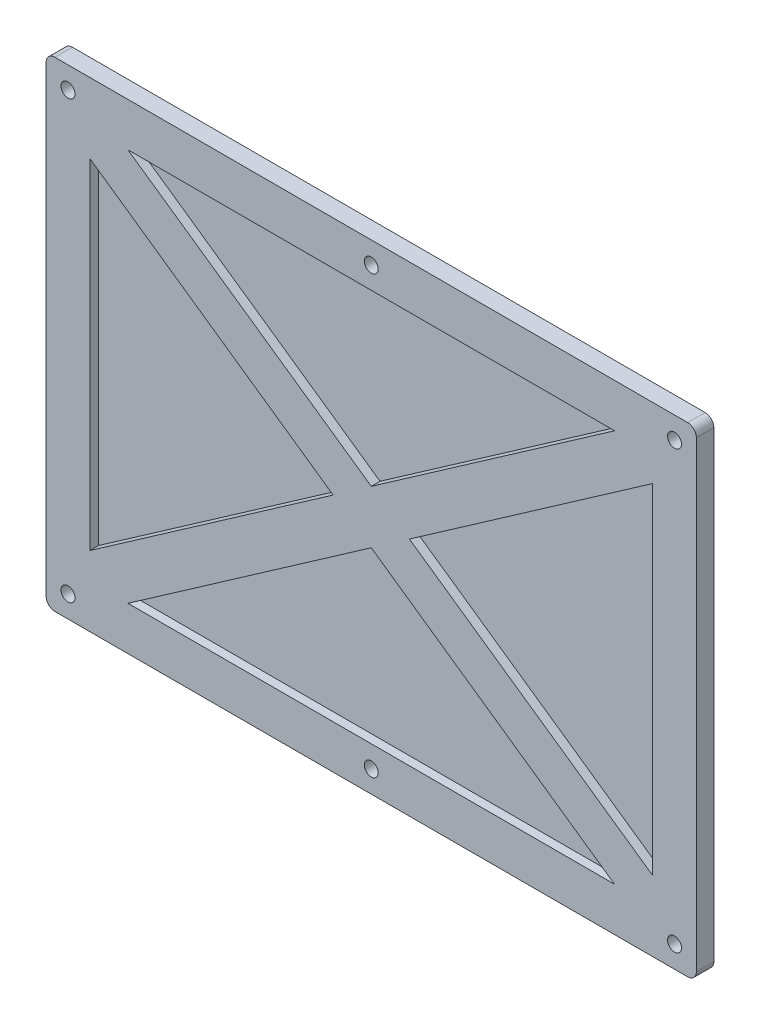
SolidWorks part; units mm, degrees
ref_plane "Přední rovina" through (0, 0, 0) normal (0, 0, 1) x (1, 0, 0)
ref_plane "Horní rovina" through (0, 0, 0) normal (0, 1, 0) x (1, 0, 0)
ref_plane "Pravá rovina" through (0, 0, 0) normal (1, 0, 0) x (0, 0, -1)
sketch "Skica1" plane through (0, 0, 0) normal (0, 0, 1) x (1, 0, 0)
  line L1 (-74.5, -55) -> (74.5, -55)
  line L2 (-74.5, -55) -> (-74.5, 55)
  line L3 (-74.5, 55) -> (74.5, 55)
  line L4 (74.5, -55) -> (74.5, 55)
  line L5 (-74.5, -55) -> (74.5, 55) construction
  line L6 (-74.5, 55) -> (74.5, -55) construction
  line L7 (-69.5, -50) -> (69.5, -50) construction
  line L8 (-69.5, -50) -> (-69.5, 50) construction
  line L9 (-69.5, 50) -> (69.5, 50) construction
  line L10 (69.5, -50) -> (69.5, 50) construction
  line L11 (-69.5, -50) -> (69.5, 50) construction
  line L12 (-69.5, 50) -> (69.5, -50) construction
  circle A0 centre (-69.5, 50) radius 1.6
  circle A1 centre (69.5, 50) radius 1.6
  circle A2 centre (69.5, -50) radius 1.6
  circle A3 centre (-69.5, -50) radius 1.6
  circle A4 centre (0, 50) radius 1.6
  circle A5 centre (0, -50) radius 1.6
  point P0 (0, 0)
  point P6 (0, 0)
  dimension "D5" = 3.2
  dimension "D1" = 110
  dimension "D2" = 149
  dimension "D3" = 5
  dimension "D4" = 5
extrude "Přidat vysunutím1" add sketch "Skica1" along normal blind 2
sketch "Skica2" plane through (0, 0, 2) normal (0, 0, 1) x (1, 0, 0)
  line L0 (74.5, 55) -> (-74.5, 55) construction
  line L1 (55.7615, -45) -> (-55.7615, -45)
  line L2 (64.5, -38.9034) -> (64.5, 38.9034)
  line L3 (55.7615, 45) -> (-55.7615, 45)
  line L4 (-64.5, -38.9034) -> (-64.5, 38.9034)
  line L5 (64.5, -45) -> (-64.5, 45) construction
  line L6 (64.5, 45) -> (-64.5, -45) construction
  line L7 (-74.5, 55) -> (-74.5, -55) construction
  line L8 (-8.7385, 0) -> (-64.5, 38.9034)
  line L9 (74.5, -55) -> (74.5, 55) construction
  line L10 (-74.5, -55) -> (74.5, -55) construction
  line L11 (74.5, -55) -> (74.5, 55)
  line L12 (-74.5, -55) -> (74.5, -55)
  line L13 (-74.5, 55) -> (-74.5, -55)
  line L14 (74.5, 55) -> (-74.5, 55)
  line L15 (-55.7615, 45) -> (0, 6.0966)
  line L16 (55.7615, -45) -> (0, -6.0966)
  line L17 (-64.5, -38.9034) -> (-8.7385, 0)
  line L18 (64.5, 38.9034) -> (8.7385, 0)
  line L19 (0, 6.0966) -> (55.7615, 45)
  line L20 (8.7385, 0) -> (64.5, -38.9034)
  line L21 (0, -6.0966) -> (-55.7615, -45)
  circle A0 centre (-69.5, -50) radius 1.6 construction
  circle A1 centre (69.5, -50) radius 1.6 construction
  circle A2 centre (69.5, 50) radius 1.6 construction
  circle A3 centre (-69.5, 50) radius 1.6 construction
  circle A4 centre (-69.5, -50) radius 1.6
  circle A5 centre (69.5, -50) radius 1.6
  circle A6 centre (69.5, 50) radius 1.6
  circle A7 centre (-69.5, 50) radius 1.6
  circle A8 centre (0, -50) radius 1.6 construction
  circle A9 centre (0, 50) radius 1.6 construction
  circle A10 centre (0, -50) radius 1.6
  circle A11 centre (0, 50) radius 1.6
  point P12 (0, 0)
  point P30 (-64.5, -34.8883)
  dimension "D1" = 10
  dimension "D2" = 10
  dimension "D3" = 10
  dimension "D4" = 10
  dimension "D5" = 5
  dimension "D6" = 5
extrude "Přidat vysunutím2" add sketch "Skica2" along normal blind 2
fillet "Zaoblit1" radius 2 4 edges at (-74.5, -55, 2) (74.5, -55, 2) (74.5, 55, 2) (-74.5, 55, 2)
